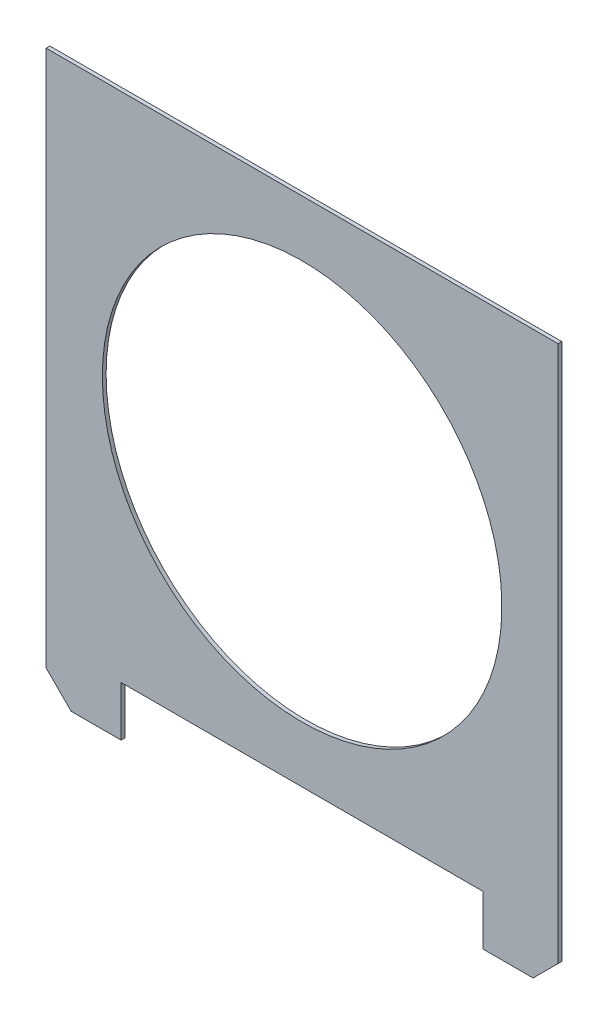
SolidWorks part; units mm, degrees
ref_plane "Plan de face" through (0, 0, 0) normal (0, 0, 1) x (1, 0, 0)
ref_plane "Plan de dessus" through (0, 0, 0) normal (0, 1, 0) x (1, 0, 0)
ref_plane "Plan de droite" through (0, 0, 0) normal (1, 0, 0) x (0, 0, -1)
sketch "Esquisse1" plane through (0, 0, 0) normal (0, 0, 1) x (1, 0, 0)
  line L1 (-20.5, -20.5) -> (20.5, -20.5)
  line L2 (-20.5, -20.5) -> (-20.5, 20.5)
  line L3 (-20.5, 20.5) -> (20.5, 20.5)
  line L4 (20.5, -20.5) -> (20.5, 20.5)
  line L5 (-20.5, -20.5) -> (20.5, 20.5) construction
  line L6 (-20.5, 20.5) -> (20.5, -20.5) construction
  point P0 (0, 0)
  dimension "D1" = 41
  dimension "D2" = 41
extrude "Boss.-Extru.1" add sketch "Esquisse1" along normal blind 0.3
sketch "Esquisse2" plane through (0, 0, 0) normal (0, 0, -1) x (-1, 0, 0)
  line L0 (0, -4.737) -> (0, -16.9551) construction
  line L1 (20.5, 20.5) -> (14.5, 20.5)
  line L2 (20.5, 20.5) -> (20.5, 24.5)
  line L3 (20.5, 24.5) -> (14.5, 24.5)
  line L4 (14.5, 20.5) -> (14.5, 24.5)
  line L5 (-20.5, -20.5) -> (-14.5, -20.5)
  line L6 (-20.5, -20.5) -> (-20.5, -24.5)
  line L7 (-20.5, -24.5) -> (-14.5, -24.5)
  line L8 (-14.5, -20.5) -> (-14.5, -24.5)
  line L9 (20.5, -24.5) -> (14.5, -24.5)
  line L10 (14.5, -20.5) -> (14.5, -24.5)
  line L11 (20.5, -20.5) -> (14.5, -20.5)
  line L12 (20.5, -20.5) -> (20.5, -24.5)
  dimension "D1" = 6
  dimension "D2" = 4
  dimension "D3" = 4
  dimension "D4" = 6
extrude "Boss.-Extru.2" add sketch "Esquisse2" against normal up to surface (0.3 mm away) up to face at (0, 0, 0.3)
sketch "Esquisse3" plane through (0, 0, 0) normal (0, 0, -1) x (-1, 0, 0)
  circle A0 centre (0, 0) radius 12.5
  dimension "D1" = 25
extrude "Enlèv. mat.-Extru.1" cut sketch "Esquisse3" against normal through all
sketch "Esquisse4" plane through (0, 0, 0) normal (0, 0, -1) x (-1, 0, 0)
  circle A0 centre (0, 0) radius 16
  dimension "D1" = 32
extrude "Enlèv. mat.-Extru.2" cut sketch "Esquisse4" against normal through all
chamfer "Chanfrein1" distance 2 angle 45 1 edges at (-20.5, -24.5, 0.15)
chamfer "Chanfrein2" distance 2 angle 45 1 edges at (20.5, -24.5, 0.15)
sketch "Esquisse6" plane through (0, 0, 0) normal (0, 0, -1) x (-1, 0, 0)
  line L0 (20.5, 24.5) -> (20.5, -22.5) construction
  line L1 (14.5, 24.5) -> (20.5, 24.5)
  line L2 (14.5, 24.5) -> (14.5, 20.5)
  line L3 (14.5, 20.5) -> (20.5, 20.5)
  line L4 (20.5, 24.5) -> (20.5, 20.5)
  point P7 (0, 0)
extrude "Enlèv. mat.-Extru.4" cut sketch "Esquisse6" against normal through all
